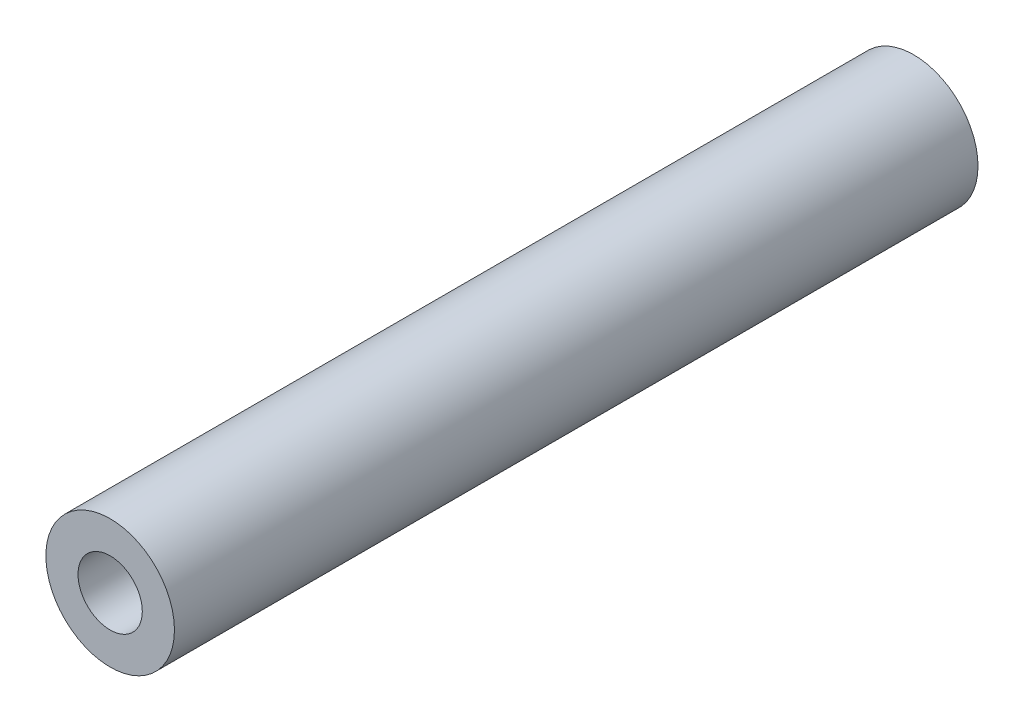
SolidWorks part; units mm, degrees
ref_plane "前视基准面" through (0, 0, 0) normal (0, 0, 1) x (1, 0, 0)
ref_plane "上视基准面" through (0, 0, 0) normal (0, 1, 0) x (1, 0, 0)
ref_plane "右视基准面" through (0, 0, 0) normal (1, 0, 0) x (0, 0, -1)
sketch "草图1" plane through (0, 0, 0) normal (0, 0, 1) x (1, 0, 0)
  circle A0 centre (0, 0) radius 1
  circle A1 centre (0, 0) radius 2
  dimension "D1" = 4
  dimension "D2" = 2
extrude "凸台-拉伸1" add sketch "草图1" along normal mid plane 25
